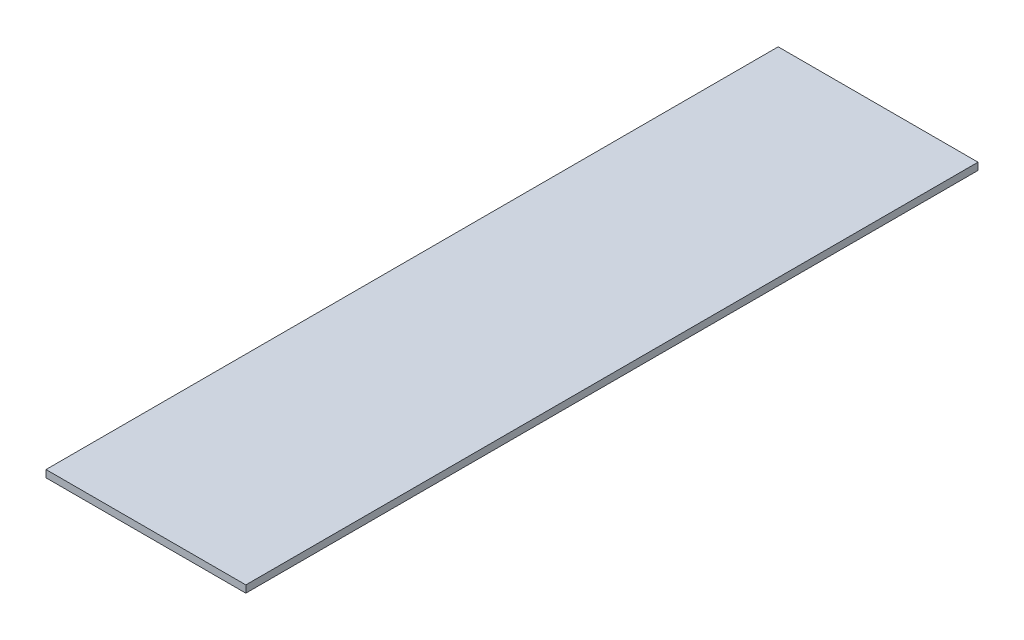
SolidWorks part; units mm, degrees
material "Custom Plastic"
ref_plane "Front Plane" through (0, 0, 0) normal (0, 0, 1) x (1, 0, 0)
ref_plane "Top Plane" through (0, 0, 0) normal (0, 1, 0) x (1, 0, 0)
ref_plane "Right Plane" through (0, 0, 0) normal (1, 0, 0) x (0, 0, -1)
sketch "Sketch1" plane through (0, 0, 0) normal (0, 1, 0) x (1, 0, 0)
  line L0 (0, 200.7296) -> (0, 39.3856) construction
  line L1 (-12.5, 200.7296) -> (12.5, 200.7296)
  line L2 (-12.5, 200.7296) -> (-12.5, 109.1296)
  line L3 (-12.5, 109.1296) -> (12.5, 109.1296)
  line L4 (12.5, 200.7296) -> (12.5, 109.1296)
  point P7 (0, 109.1296)
  dimension "D1" = 25
  dimension "D3" = 109.1296
  dimension "D4" = 91.6
extrude "Boss-Extrude1" add sketch "Sketch1" along normal blind 0.9
